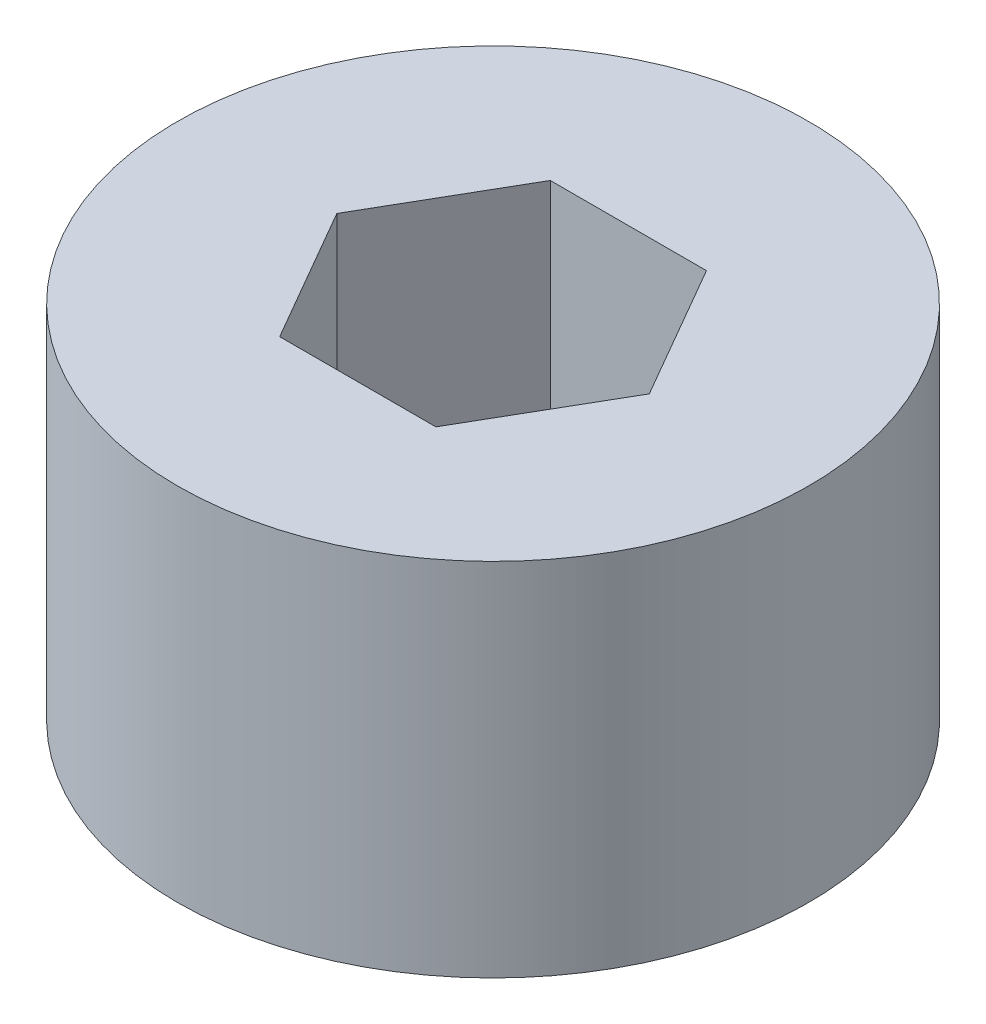
SolidWorks part; units mm, degrees
ref_plane "Front Plane" through (0, 0, 0) normal (0, 0, 1) x (1, 0, 0)
ref_plane "Top Plane" through (0, 0, 0) normal (0, 1, 0) x (1, 0, 0)
ref_plane "Right Plane" through (0, 0, 0) normal (1, 0, 0) x (0, 0, -1)
sketch "Sketch1" plane through (0, 0, 0) normal (0, 1, 0) x (1, 0, 0)
  circle A0 centre (0, 0) radius 3.5
  dimension "D1" = 7
extrude "Boss-Extrude1" add sketch "Sketch1" along normal blind 4
sketch "Sketch2" plane through (0, 0, 0) normal (0, -1, 0) x (1, 0, 0)
  circle A0 centre (0, 0) radius 2
  dimension "D1" = 4
extrude "Boss-Extrude2" add sketch "Sketch2" along normal blind 1
sketch "Sketch3" plane through (0, 4, 0) normal (0, 1, 0) x (1, 0, 0)
  line L1 (1.7321, 0) -> (0.866, 1.5)
  line L2 (0.866, 1.5) -> (-0.866, 1.5)
  line L3 (-0.866, 1.5) -> (-1.7321, 0)
  line L4 (-1.7321, 0) -> (-0.866, -1.5)
  line L5 (-0.866, -1.5) -> (0.866, -1.5)
  line L6 (0.866, -1.5) -> (1.7321, 0)
  circle A0 centre (0, 0) radius 1.5 construction
  dimension "D1" = 3
extrude "Cut-Extrude1" cut sketch "Sketch3" against normal blind 3
